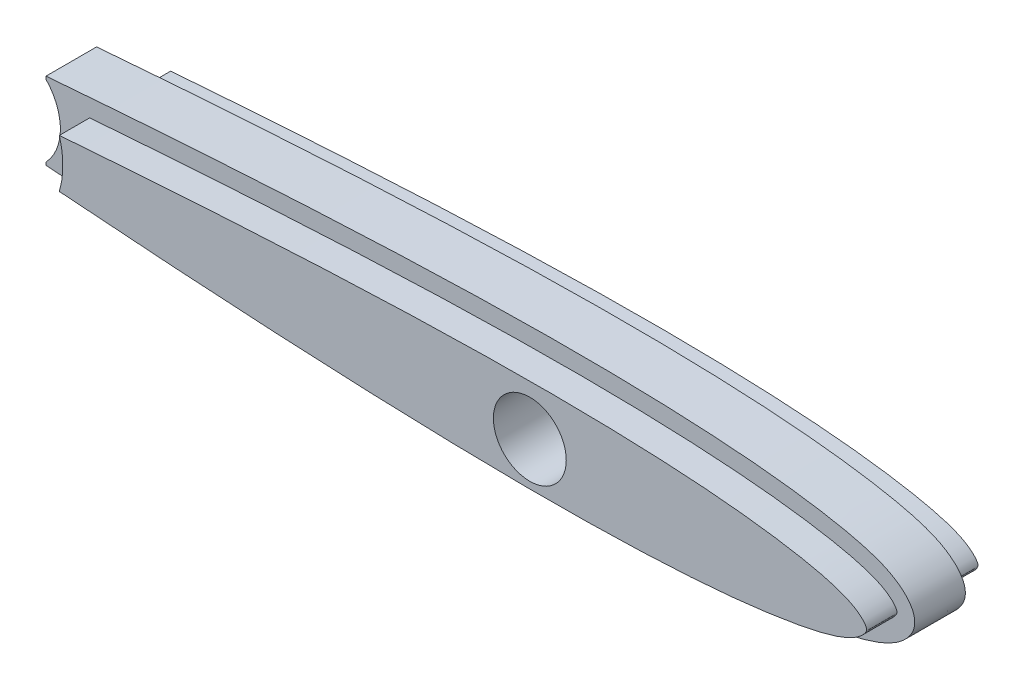
SolidWorks part; units mm, degrees
ref_plane "Front Plane" through (0, 0, 0) normal (0, 0, 1) x (1, 0, 0)
ref_plane "Top Plane" through (0, 0, 0) normal (0, 1, 0) x (1, 0, 0)
ref_plane "Right Plane" through (0, 0, 0) normal (1, 0, 0) x (0, 0, -1)
sketch "Sketch1" plane through (0, 0, 0) normal (0, 0, 1) x (1, 0, 0)
  line L4 (-706.7938, 2.2504) -> (-706.7938, 1.9715)
  line L5 (-706.7938, -5.0985) -> (-706.7938, -5.3802)
  arc A2 (-706.7938, -5.0985) -> (-706.7938, 1.9715) centre (-710.4884, -1.5635) ccw
  spline S2 degree 3 poles (-706.7938, -5.3802) (-704.1764, -5.592) (-696.7883, -6.161) (-687.0049, -6.8148) (-677.4434, -7.3285) (-670.2656, -7.6378) (-663.0802, -7.8569) (-655.8863, -7.9601) (-649.8823, -7.9158) (-645.0737, -7.7768) (-641.4661, -7.6099) (-637.8546, -7.3655) (-634.8408, -7.0787) (-632.4293, -6.7787) (-630.6227, -6.5149) (-628.8123, -6.2021) (-627.3003, -5.8875) (-626.0753, -5.5773) (-625.1447, -5.2998) (-624.2018, -4.9578) (-623.3964, -4.5815) (-622.7483, -4.1895) (-622.2645, -3.8332) (-621.8884, -3.491) (-621.5737, -3.1399) (-621.3353, -2.8044) (-621.1521, -2.4704) (-621.0138, -2.0627) (-620.9486, -1.6664) (-620.9784, -1.2185) (-621.1027, -0.7699) (-621.2898, -0.3987) (-621.521, -0.0562) (-621.8417, 0.3166) (-622.2137, 0.6613) (-622.6971, 1.026) (-623.3445, 1.425) (-624.151, 1.8078) (-625.0951, 2.1542) (-626.0263, 2.4345) (-626.9455, 2.6693) (-628.1602, 2.941) (-629.6699, 3.228) (-631.478, 3.5155) (-633.8879, 3.8423) (-636.9036, 4.1569) (-640.5153, 4.4246) (-644.124, 4.6097) (-647.7316, 4.7298) (-652.5348, 4.8177) (-658.5378, 4.8077) (-665.7281, 4.6591) (-672.9103, 4.4042) (-680.0859, 4.0652) (-689.6443, 3.5193) (-698.5452, 2.9014) (-705.0549, 2.3911) (-706.7938, 2.2504) knots 0.161072 0.161072 0.161072 0.161072 0.19714 0.26286 0.29572 0.32858 0.36144 0.394299 0.427159 0.443589 0.460019 0.476449 0.492879 0.501094 0.509309 0.517524 0.525739 0.529846 0.533954 0.538061 0.542169 0.544222 0.546276 0.54833 0.549357 0.550383 0.55141 0.551924 0.552437 0.552951 0.553464 0.554491 0.555518 0.556545 0.558598 0.560652 0.562706 0.566813 0.570921 0.575028 0.579136 0.583243 0.591458 0.599673 0.607888 0.624318 0.640748 0.657178 0.673608 0.690038 0.722898 0.755757 0.788617 0.821477 0.854337 0.920056 0.944018 0.944018 0.944018 0.944018
extrude "Boss-Extrude1" add sketch "Sketch1" along normal blind 5
sketch "Sketch2" plane through (0, 0, 0) normal (0, 0, -1) x (-1, 0, 0)
  circle A0 centre (655.9929, -1.9195) radius 3.6 construction
  circle A1 centre (655.9929, -1.9195) radius 3.6
extrude "Cut-Extrude1" cut sketch "Sketch2" against normal blind 5
sketch "Sketch3" plane through (0, 0, 5) normal (0, 0, 1) x (1, 0, 0)
  arc A1 (-702.6192, -3.5388) -> (-702.3751, -1.5605) centre (-710.4884, -1.5635) ccw construction
  arc A2 (-702.8119, -4.1898) -> (-702.8111, 1.0606) centre (-710.4884, -1.5635) ccw
  circle A3 centre (-655.9929, -1.9195) radius 3.6 construction
  circle A4 centre (-655.9929, -1.9195) radius 3.6
  spline S0 degree 3 poles (-1458.7742, 1754.4211) (-1395.7984, 224.9146) (-1050.7374, 19.6539) (-690.3603, -5.0851) (-683.4721, -5.506) (-676.464, -5.8734) (-669.4557, -6.1656) (-663.6689, -6.3344) (-659.1295, -6.4119) (-655.8271, -6.4395) (-652.6128, -6.4356) (-649.5004, -6.3942) (-646.5035, -6.3216) (-643.6351, -6.2119) (-640.9073, -6.0692) (-638.3314, -5.89) (-635.9183, -5.6775) (-633.6791, -5.4298) (-631.6233, -5.1516) (-629.7587, -4.8501) (-628.0933, -4.5266) (-626.6323, -4.1822) (-625.3828, -3.8054) (-624.3473, -3.3891) (-623.5355, -2.9298) (-622.9517, -2.4503) (-622.5871, -2.0107) (-622.4112, -1.5647) (-622.5871, -1.1186) (-622.9517, -0.6791) (-623.5355, -0.1995) (-624.3473, 0.2598) (-625.3828, 0.676) (-626.6323, 1.0529) (-628.0933, 1.3972) (-629.7587, 1.7207) (-631.6233, 2.0223) (-633.6791, 2.3005) (-635.9183, 2.5482) (-638.3314, 2.7607) (-640.9073, 2.9399) (-643.6351, 3.0826) (-646.5035, 3.1923) (-649.5004, 3.2649) (-652.6128, 3.3063) (-655.8271, 3.3101) (-659.1295, 3.2826) (-663.6689, 3.2051) (-669.4557, 3.0363) (-676.464, 2.7441) (-683.4721, 2.3767) (-690.3603, 1.9557) (-1049.5872, -22.7043) (-1393.5841, -226.7065) (-1455.9917, -1759.2228) knots -4.752348 -4.752348 -4.752348 -4.752348 0.15349 0.184227 0.21605 0.248408 0.28075 0.312527 0.328033 0.343195 0.357951 0.372242 0.386007 0.399183 0.411723 0.423576 0.434697 0.44504 0.454559 0.463229 0.471015 0.477891 0.483866 0.488952 0.493207 0.496652 0.499261 0.501069 0.502876 0.505486 0.508931 0.513186 0.518272 0.524247 0.531123 0.538909 0.547579 0.557098 0.567441 0.578562 0.590415 0.602955 0.616131 0.629896 0.644187 0.658943 0.674105 0.689611 0.721388 0.75373 0.786088 0.817911 0.848648 5.738628 5.738628 5.738628 5.738628 only from (-702.8119, -4.1898) to (-702.8111, 1.0606) construction
  spline S1 degree 3 poles (-702.8119, -4.1898) (-700.9173, -4.3362) (-696.7938, -4.6434) (-690.3603, -5.0851) (-683.4721, -5.506) (-676.464, -5.8734) (-669.4557, -6.1656) (-663.6689, -6.3344) (-659.1295, -6.4119) (-655.8271, -6.4395) (-652.6128, -6.4356) (-649.5004, -6.3942) (-646.5035, -6.3216) (-643.6351, -6.2119) (-640.9073, -6.0692) (-638.3314, -5.89) (-635.9183, -5.6775) (-633.6791, -5.4298) (-631.6233, -5.1516) (-629.7587, -4.8501) (-628.0933, -4.5266) (-626.6323, -4.1822) (-625.3828, -3.8054) (-624.3473, -3.3891) (-623.5355, -2.9298) (-622.9517, -2.4503) (-622.5871, -2.0107) (-622.4112, -1.5647) (-622.5871, -1.1186) (-622.9517, -0.6791) (-623.5355, -0.1995) (-624.3473, 0.2598) (-625.3828, 0.676) (-626.6323, 1.0529) (-628.0933, 1.3972) (-629.7587, 1.7207) (-631.6233, 2.0223) (-633.6791, 2.3005) (-635.9183, 2.5482) (-638.3314, 2.7607) (-640.9073, 2.9399) (-643.6351, 3.0826) (-646.5035, 3.1923) (-649.5004, 3.2649) (-652.6128, 3.3063) (-655.8271, 3.3101) (-659.1295, 3.2826) (-663.6689, 3.2051) (-669.4557, 3.0363) (-676.464, 2.7441) (-683.4721, 2.3767) (-690.3603, 1.9557) (-696.7935, 1.5141) (-700.9168, 1.207) (-702.8111, 1.0606) knots 0.127353 0.127353 0.127353 0.127353 0.15349 0.184227 0.21605 0.248408 0.28075 0.312527 0.328033 0.343195 0.357951 0.372242 0.386007 0.399183 0.411723 0.423576 0.434697 0.44504 0.454559 0.463229 0.471015 0.477891 0.483866 0.488952 0.493207 0.496652 0.499261 0.501069 0.502876 0.505486 0.508931 0.513186 0.518272 0.524247 0.531123 0.538909 0.547579 0.557098 0.567441 0.578562 0.590415 0.602955 0.616131 0.629896 0.644187 0.658943 0.674105 0.689611 0.721388 0.75373 0.786088 0.817911 0.848648 0.874781 0.874781 0.874781 0.874781
extrude "Boss-Extrude2" add sketch "Sketch3" along normal blind 3
sketch "Sketch4" plane through (0, 0, 0) normal (0, 0, -1) x (-1, 0, 0)
  circle A0 centre (655.9929, -1.9195) radius 3.6 construction
  arc A1 (702.8111, 1.0606) -> (702.8119, -4.1898) centre (710.4884, -1.5635) ccw
  arc A2 (702.8111, 1.0606) -> (702.8119, -4.1898) centre (710.4884, -1.5635) ccw
  circle A3 centre (655.9929, -1.9195) radius 3.6
  spline S1 degree 3 poles (1460.1118, -2759.1755) (1520.2418, -308.2066) (1115.5237, -27.2307) (690.3603, 1.9557) (683.4721, 2.3767) (676.464, 2.7441) (669.4557, 3.0363) (663.6689, 3.2051) (659.1295, 3.2826) (655.8271, 3.3101) (652.6128, 3.3063) (649.5004, 3.2649) (646.5035, 3.1923) (643.6351, 3.0826) (640.9073, 2.9399) (638.3314, 2.7607) (635.9183, 2.5482) (633.6791, 2.3005) (631.6233, 2.0223) (629.7587, 1.7207) (628.0933, 1.3972) (626.6323, 1.0529) (625.3828, 0.676) (624.3473, 0.2598) (623.5355, -0.1995) (622.9517, -0.6791) (622.5871, -1.1186) (622.4112, -1.5647) (622.5871, -2.0107) (622.9517, -2.4503) (623.5355, -2.9298) (624.3473, -3.3891) (625.3828, -3.8054) (626.6323, -4.1822) (628.0933, -4.5266) (629.7587, -4.8501) (631.6233, -5.1516) (633.6791, -5.4298) (635.9183, -5.6775) (638.3314, -5.89) (640.9073, -6.0692) (643.6351, -6.2119) (646.5035, -6.3216) (649.5004, -6.3942) (652.6128, -6.4356) (655.8271, -6.4395) (659.1295, -6.4119) (663.6689, -6.3344) (669.4557, -6.1656) (676.464, -5.8734) (683.4721, -5.506) (690.3603, -5.0851) (1117.011, 24.2034) (1523.0847, 307.0859) (1463.1046, 2754.3608) knots -5.645538 -5.645538 -5.645538 -5.645538 0.153487 0.184223 0.216047 0.248405 0.280746 0.312524 0.328029 0.343192 0.357947 0.372239 0.386003 0.399179 0.41172 0.423573 0.434693 0.445036 0.454556 0.463225 0.471011 0.477887 0.483862 0.488948 0.493204 0.496648 0.499258 0.501066 0.502873 0.505483 0.508927 0.513183 0.518269 0.524244 0.53112 0.538906 0.547575 0.557095 0.567438 0.578558 0.590411 0.602952 0.616128 0.629892 0.644184 0.658939 0.674102 0.689607 0.721385 0.753726 0.786084 0.817908 0.848644 6.668173 6.668173 6.668173 6.668173 only from (702.8111, 1.0606) to (702.8119, -4.1898)
  spline S2 degree 3 poles (702.8111, 1.0606) (700.9168, 1.207) (696.7935, 1.5141) (690.3603, 1.9557) (683.4721, 2.3767) (676.464, 2.7441) (669.4557, 3.0363) (663.6689, 3.2051) (659.1295, 3.2826) (655.8271, 3.3101) (652.6128, 3.3063) (649.5004, 3.2649) (646.5035, 3.1923) (643.6351, 3.0826) (640.9073, 2.9399) (638.3314, 2.7607) (635.9183, 2.5482) (633.6791, 2.3005) (631.6233, 2.0223) (629.7587, 1.7207) (628.0933, 1.3972) (626.6323, 1.0529) (625.3828, 0.676) (624.3473, 0.2598) (623.5355, -0.1995) (622.9517, -0.6791) (622.5871, -1.1186) (622.4112, -1.5647) (622.5871, -2.0107) (622.9517, -2.4503) (623.5355, -2.9298) (624.3473, -3.3891) (625.3828, -3.8054) (626.6323, -4.1822) (628.0933, -4.5266) (629.7587, -4.8501) (631.6233, -5.1516) (633.6791, -5.4298) (635.9183, -5.6775) (638.3314, -5.89) (640.9073, -6.0692) (643.6351, -6.2119) (646.5035, -6.3216) (649.5004, -6.3942) (652.6128, -6.4356) (655.8271, -6.4395) (659.1295, -6.4119) (663.6689, -6.3344) (669.4557, -6.1656) (676.464, -5.8734) (683.4721, -5.506) (690.3603, -5.0851) (696.7938, -4.6434) (700.9173, -4.3362) (702.8119, -4.1898) knots 0.127353 0.127353 0.127353 0.127353 0.153487 0.184223 0.216047 0.248405 0.280746 0.312524 0.328029 0.343192 0.357947 0.372239 0.386003 0.399179 0.41172 0.423573 0.434693 0.445036 0.454556 0.463225 0.471011 0.477887 0.483862 0.488948 0.493204 0.496648 0.499258 0.501066 0.502873 0.505483 0.508927 0.513183 0.518269 0.524244 0.53112 0.538906 0.547575 0.557095 0.567438 0.578558 0.590411 0.602952 0.616128 0.629892 0.644184 0.658939 0.674102 0.689607 0.721385 0.753726 0.786084 0.817908 0.848644 0.874781 0.874781 0.874781 0.874781
  dimension "D1" = 0
extrude "Boss-Extrude3" add sketch "Sketch4" along normal blind 3
sketch "Sketch5" plane through (0, 0, -3) normal (0, 0, -1) x (-1, 0, 0)
  line L2 (706.7938, -5.3802) -> (706.7938, -5.0985)
  line L3 (706.7938, 1.9715) -> (706.7938, 2.2504)
  line L4 (706.7938, -5.3802) -> (706.7938, -5.0985)
  line L5 (706.7938, 1.9715) -> (706.7938, 2.2504)
  arc A2 (702.4766, 0.8356) -> (702.4772, -3.9649) centre (710.4884, -1.5635) ccw
  arc A3 (702.4766, 0.8356) -> (702.4772, -3.9649) centre (710.4884, -1.5635) ccw
  arc A4 (706.7938, 1.9715) -> (706.7938, -5.0985) centre (710.4884, -1.5635) ccw
  arc A5 (706.7938, 1.9715) -> (706.7938, -5.0985) centre (710.4884, -1.5635) ccw
  spline S2 degree 3 poles (1843.7159, 2649.2362) (1372.5351, -266.0132) (1032.1024, -17.1061) (678.7978, 2.3749) (675.4128, 2.5393) (668.6404, 2.8098) (665.2531, 2.917) (658.475, 3.0498) (655.0844, 3.078) (648.2979, 3.0053) (644.9038, 2.9112) (639.8233, 2.621) (638.1312, 2.4986) (634.751, 2.1792) (633.0639, 1.9804) (630.5477, 1.5977) (629.7112, 1.4561) (628.0447, 1.1285) (627.2139, 0.9453) (625.9909, 0.5988) (625.587, 0.4707) (624.7922, 0.1711) (624.3988, -0.0022) (623.8487, -0.3177) (623.6716, -0.4326) (623.3346, -0.6888) (623.1729, -0.8307) (622.9559, -1.0706) (622.8886, -1.1558) (622.804, -1.2931) (622.7781, -1.3403) (622.7348, -1.4396) (622.717, -1.4915) (622.709, -1.5992) (622.7228, -1.6527) (622.7603, -1.7528) (622.7846, -1.8004) (622.8648, -1.9397) (622.9288, -2.0251) (623.1369, -2.2644) (623.2962, -2.4077) (623.6298, -2.6678) (623.8052, -2.7841) (624.3498, -3.1032) (624.7389, -3.2776) (625.5232, -3.5783) (625.9213, -3.7065) (626.7242, -3.9375) (627.1291, -4.0403) (628.3501, -4.3248) (629.1725, -4.485) (630.8241, -4.7726) (631.6512, -4.8988) (634.1352, -5.2407) (635.7949, -5.4173) (639.1193, -5.7021) (640.7838, -5.8118) (645.7827, -6.0697) (649.1232, -6.1521) (655.8065, -6.2041) (659.1455, -6.1704) (665.8205, -6.0299) (669.1563, -5.921) (675.8257, -5.6494) (679.1591, -5.4856) (1033.4659, 14.1921) (1374.5921, 263.2311) (1846.3765, -2650.3425) knots -6.337659 -6.337659 -6.337659 -6.337659 0.125 0.125 0.1875 0.1875 0.25 0.25 0.3125 0.3125 0.375 0.375 0.40625 0.40625 0.4375 0.4375 0.453125 0.453125 0.46875 0.46875 0.476563 0.476563 0.484375 0.484375 0.488281 0.488281 0.492188 0.492188 0.494141 0.494141 0.495117 0.495117 0.496094 0.496094 0.49707 0.49707 0.498047 0.498047 0.5 0.5 0.503906 0.503906 0.507813 0.507813 0.515625 0.515625 0.523438 0.523438 0.53125 0.53125 0.546875 0.546875 0.5625 0.5625 0.59375 0.59375 0.625 0.625 0.6875 0.6875 0.75 0.75 0.8125 0.8125 0.875 0.875 7.457326 7.457326 7.457326 7.457326 only from (702.4766, 0.8356) to (702.4772, -3.9649)
  spline S3 degree 3 poles (702.4766, 0.8356) (695.7145, 1.3561) (688.95, 1.8152) (678.7978, 2.3749) (675.4128, 2.5393) (668.6404, 2.8098) (665.2531, 2.917) (658.475, 3.0498) (655.0844, 3.078) (648.2979, 3.0053) (644.9038, 2.9112) (639.8233, 2.621) (638.1312, 2.4986) (634.751, 2.1792) (633.0639, 1.9804) (630.5477, 1.5977) (629.7112, 1.4561) (628.0447, 1.1285) (627.2139, 0.9453) (625.9909, 0.5988) (625.587, 0.4707) (624.7922, 0.1711) (624.3988, -0.0022) (623.8487, -0.3177) (623.6716, -0.4326) (623.3346, -0.6888) (623.1729, -0.8307) (622.9559, -1.0706) (622.8886, -1.1558) (622.804, -1.2931) (622.7781, -1.3403) (622.7348, -1.4396) (622.717, -1.4915) (622.709, -1.5992) (622.7228, -1.6527) (622.7603, -1.7528) (622.7846, -1.8004) (622.8648, -1.9397) (622.9288, -2.0251) (623.1369, -2.2644) (623.2962, -2.4077) (623.6298, -2.6678) (623.8052, -2.7841) (624.3498, -3.1032) (624.7389, -3.2776) (625.5232, -3.5783) (625.9213, -3.7065) (626.7242, -3.9375) (627.1291, -4.0403) (628.3501, -4.3248) (629.1725, -4.485) (630.8241, -4.7726) (631.6512, -4.8988) (634.1352, -5.2407) (635.7949, -5.4173) (639.1193, -5.7021) (640.7838, -5.8118) (645.7827, -6.0697) (649.1232, -6.1521) (655.8065, -6.2041) (659.1455, -6.1704) (665.8205, -6.0299) (669.1563, -5.921) (675.8257, -5.6494) (679.1591, -5.4856) (689.1568, -4.9304) (695.8183, -4.4774) (702.4772, -3.9649) knots 0 0 0 0 0.125 0.125 0.1875 0.1875 0.25 0.25 0.3125 0.3125 0.375 0.375 0.40625 0.40625 0.4375 0.4375 0.453125 0.453125 0.46875 0.46875 0.476563 0.476563 0.484375 0.484375 0.488281 0.488281 0.492188 0.492188 0.494141 0.494141 0.495117 0.495117 0.496094 0.496094 0.49707 0.49707 0.498047 0.498047 0.5 0.5 0.503906 0.503906 0.507813 0.507813 0.515625 0.515625 0.523438 0.523438 0.53125 0.53125 0.546875 0.546875 0.5625 0.5625 0.59375 0.59375 0.625 0.625 0.6875 0.6875 0.75 0.75 0.8125 0.8125 0.875 0.875 1 1 1 1
  spline S4 degree 3 poles (1427.9881, -2784.3302) (1470.56, -267.9599) (1089.4618, -24.2364) (689.6443, 3.5193) (680.0859, 4.0652) (672.9103, 4.4042) (665.7281, 4.6591) (658.5378, 4.8077) (652.5348, 4.8177) (647.7316, 4.7298) (644.124, 4.6097) (640.5153, 4.4246) (636.9036, 4.1569) (633.8879, 3.8423) (631.478, 3.5155) (629.6699, 3.228) (628.1602, 2.941) (626.9455, 2.6693) (626.0263, 2.4345) (625.0951, 2.1542) (624.151, 1.8078) (623.3445, 1.425) (622.6971, 1.026) (622.2137, 0.6613) (621.8417, 0.3166) (621.521, -0.0562) (621.2898, -0.3987) (621.1027, -0.7699) (620.9784, -1.2185) (620.9486, -1.6664) (621.0138, -2.0627) (621.1521, -2.4704) (621.3353, -2.8044) (621.5737, -3.1399) (621.8884, -3.491) (622.2645, -3.8332) (622.7483, -4.1895) (623.3964, -4.5815) (624.2018, -4.9578) (625.1447, -5.2998) (626.0753, -5.5773) (627.3003, -5.8875) (628.8123, -6.2021) (630.6227, -6.5149) (632.4293, -6.7787) (634.8408, -7.0787) (637.8546, -7.3655) (641.4661, -7.6099) (645.0737, -7.7768) (649.8823, -7.9158) (655.8863, -7.9601) (663.0802, -7.8569) (670.2656, -7.6378) (677.4434, -7.3285) (687.0049, -6.8148) (1039.6939, 16.7536) (1372.7561, 207.9404) (2635.5245, 2240.3202) knots -5.220774 -5.220774 -5.220774 -5.220774 0.185033 0.250752 0.283612 0.316472 0.349332 0.382192 0.415052 0.431481 0.447911 0.464341 0.480771 0.497201 0.505416 0.513631 0.521846 0.525953 0.530061 0.534168 0.538276 0.542383 0.544437 0.546491 0.548545 0.549571 0.550598 0.551625 0.552139 0.552652 0.553165 0.553679 0.554706 0.555733 0.55676 0.558813 0.560867 0.562921 0.567028 0.571136 0.575243 0.579351 0.587566 0.595781 0.603995 0.61221 0.62864 0.64507 0.6615 0.67793 0.71079 0.74365 0.77651 0.809369 0.842229 0.907949 5.663443 5.663443 5.663443 5.663443 only from (706.7938, 2.2504) to (706.7938, -5.3802)
  spline S5 degree 3 poles (706.7938, 2.2504) (705.0549, 2.3911) (698.5452, 2.9014) (689.6443, 3.5193) (680.0859, 4.0652) (672.9103, 4.4042) (665.7281, 4.6591) (658.5378, 4.8077) (652.5348, 4.8177) (647.7316, 4.7298) (644.124, 4.6097) (640.5153, 4.4246) (636.9036, 4.1569) (633.8879, 3.8423) (631.478, 3.5155) (629.6699, 3.228) (628.1602, 2.941) (626.9455, 2.6693) (626.0263, 2.4345) (625.0951, 2.1542) (624.151, 1.8078) (623.3445, 1.425) (622.6971, 1.026) (622.2137, 0.6613) (621.8417, 0.3166) (621.521, -0.0562) (621.2898, -0.3987) (621.1027, -0.7699) (620.9784, -1.2185) (620.9486, -1.6664) (621.0138, -2.0627) (621.1521, -2.4704) (621.3353, -2.8044) (621.5737, -3.1399) (621.8884, -3.491) (622.2645, -3.8332) (622.7483, -4.1895) (623.3964, -4.5815) (624.2018, -4.9578) (625.1447, -5.2998) (626.0753, -5.5773) (627.3003, -5.8875) (628.8123, -6.2021) (630.6227, -6.5149) (632.4293, -6.7787) (634.8408, -7.0787) (637.8546, -7.3655) (641.4661, -7.6099) (645.0737, -7.7768) (649.8823, -7.9158) (655.8863, -7.9601) (663.0802, -7.8569) (670.2656, -7.6378) (677.4434, -7.3285) (687.0049, -6.8148) (696.7883, -6.161) (704.1764, -5.592) (706.7938, -5.3802) knots 0.161072 0.161072 0.161072 0.161072 0.185033 0.250752 0.283612 0.316472 0.349332 0.382192 0.415052 0.431481 0.447911 0.464341 0.480771 0.497201 0.505416 0.513631 0.521846 0.525953 0.530061 0.534168 0.538276 0.542383 0.544437 0.546491 0.548545 0.549571 0.550598 0.551625 0.552139 0.552652 0.553165 0.553679 0.554706 0.555733 0.55676 0.558813 0.560867 0.562921 0.567028 0.571136 0.575243 0.579351 0.587566 0.595781 0.603995 0.61221 0.62864 0.64507 0.6615 0.67793 0.71079 0.74365 0.77651 0.809369 0.842229 0.907949 0.944018 0.944018 0.944018 0.944018
  dimension "D1" = 0.25
  dimension "D2" = 0
extrude "Cut-Extrude2" cut sketch "Sketch5" against normal up to surface (3 mm away) up to face at (-706.4391, -2.518, 0)
sketch "Sketch6" plane through (0, 0, 8) normal (0, 0, 1) x (1, 0, 0)
  line L2 (-706.7938, -5.0985) -> (-706.7938, -5.3802)
  line L3 (-706.7938, 2.2504) -> (-706.7938, 1.9715)
  line L4 (-706.7938, -5.0985) -> (-706.7938, -5.3802)
  line L5 (-706.7938, 2.2504) -> (-706.7938, 1.9715)
  arc A1 (-702.4772, -3.9649) -> (-702.4766, 0.8356) centre (-710.4884, -1.5635) ccw
  arc A2 (-702.4772, -3.9649) -> (-702.4766, 0.8356) centre (-710.4884, -1.5635) ccw
  arc A3 (-706.7938, -5.0985) -> (-706.7938, 1.9715) centre (-710.4884, -1.5635) ccw
  arc A4 (-706.7938, -5.0985) -> (-706.7938, 1.9715) centre (-710.4884, -1.5635) ccw
  spline S1 degree 3 poles (-1846.3779, -2650.3512) (-1374.5928, 263.2316) (-1033.4663, 14.1921) (-679.1591, -5.4856) (-675.8257, -5.6494) (-669.1563, -5.921) (-665.8205, -6.0299) (-659.1455, -6.1704) (-655.8065, -6.2041) (-649.1232, -6.1521) (-645.7827, -6.0697) (-640.7838, -5.8118) (-639.1193, -5.7021) (-635.7949, -5.4173) (-634.1352, -5.2407) (-631.6512, -4.8988) (-630.8241, -4.7726) (-629.1725, -4.485) (-628.3501, -4.3248) (-627.1291, -4.0403) (-626.7242, -3.9375) (-625.9213, -3.7065) (-625.5232, -3.5783) (-624.7389, -3.2776) (-624.3498, -3.1032) (-623.8052, -2.7841) (-623.6298, -2.6678) (-623.2962, -2.4077) (-623.1369, -2.2644) (-622.9288, -2.0251) (-622.8648, -1.9397) (-622.7846, -1.8004) (-622.7603, -1.7528) (-622.7228, -1.6527) (-622.709, -1.5992) (-622.717, -1.4915) (-622.7348, -1.4396) (-622.7781, -1.3403) (-622.804, -1.2931) (-622.8886, -1.1558) (-622.9559, -1.0706) (-623.1729, -0.8307) (-623.3346, -0.6888) (-623.6716, -0.4326) (-623.8487, -0.3177) (-624.3988, -0.0022) (-624.7922, 0.1711) (-625.587, 0.4707) (-625.9909, 0.5988) (-627.2139, 0.9453) (-628.0447, 1.1285) (-629.7112, 1.4561) (-630.5477, 1.5977) (-633.0639, 1.9804) (-634.751, 2.1792) (-638.1312, 2.4986) (-639.8233, 2.621) (-644.9038, 2.9112) (-648.2979, 3.0053) (-655.0844, 3.078) (-658.475, 3.0498) (-665.2531, 2.917) (-668.6404, 2.8098) (-675.4128, 2.5393) (-678.7978, 2.3749) (-1032.1042, -17.1062) (-1372.5384, -266.0156) (-1843.7229, 2649.2791) knots -6.457333 -6.457333 -6.457333 -6.457333 0.125 0.125 0.1875 0.1875 0.25 0.25 0.3125 0.3125 0.375 0.375 0.40625 0.40625 0.4375 0.4375 0.453125 0.453125 0.46875 0.46875 0.476562 0.476562 0.484375 0.484375 0.492187 0.492187 0.496094 0.496094 0.5 0.5 0.501953 0.501953 0.50293 0.50293 0.503906 0.503906 0.504883 0.504883 0.505859 0.505859 0.507812 0.507812 0.511719 0.511719 0.515625 0.515625 0.523437 0.523437 0.53125 0.53125 0.546875 0.546875 0.5625 0.5625 0.59375 0.59375 0.625 0.625 0.6875 0.6875 0.75 0.75 0.8125 0.8125 0.875 0.875 7.337691 7.337691 7.337691 7.337691 only from (-702.4772, -3.9649) to (-702.4766, 0.8356)
  spline S2 degree 3 poles (-702.4772, -3.9649) (-695.8183, -4.4774) (-689.1568, -4.9304) (-679.1591, -5.4856) (-675.8257, -5.6494) (-669.1563, -5.921) (-665.8205, -6.0299) (-659.1455, -6.1704) (-655.8065, -6.2041) (-649.1232, -6.1521) (-645.7827, -6.0697) (-640.7838, -5.8118) (-639.1193, -5.7021) (-635.7949, -5.4173) (-634.1352, -5.2407) (-631.6512, -4.8988) (-630.8241, -4.7726) (-629.1725, -4.485) (-628.3501, -4.3248) (-627.1291, -4.0403) (-626.7242, -3.9375) (-625.9213, -3.7065) (-625.5232, -3.5783) (-624.7389, -3.2776) (-624.3498, -3.1032) (-623.8052, -2.7841) (-623.6298, -2.6678) (-623.2962, -2.4077) (-623.1369, -2.2644) (-622.9288, -2.0251) (-622.8648, -1.9397) (-622.7846, -1.8004) (-622.7603, -1.7528) (-622.7228, -1.6527) (-622.709, -1.5992) (-622.717, -1.4915) (-622.7348, -1.4396) (-622.7781, -1.3403) (-622.804, -1.2931) (-622.8886, -1.1558) (-622.9559, -1.0706) (-623.1729, -0.8307) (-623.3346, -0.6888) (-623.6716, -0.4326) (-623.8487, -0.3177) (-624.3988, -0.0022) (-624.7922, 0.1711) (-625.587, 0.4707) (-625.9909, 0.5988) (-627.2139, 0.9453) (-628.0447, 1.1285) (-629.7112, 1.4561) (-630.5477, 1.5977) (-633.0639, 1.9804) (-634.751, 2.1792) (-638.1312, 2.4986) (-639.8233, 2.621) (-644.9038, 2.9112) (-648.2979, 3.0053) (-655.0844, 3.078) (-658.475, 3.0498) (-665.2531, 2.917) (-668.6404, 2.8098) (-675.4128, 2.5393) (-678.7978, 2.3749) (-688.95, 1.8152) (-695.7145, 1.3561) (-702.4766, 0.8356) knots 0 0 0 0 0.125 0.125 0.1875 0.1875 0.25 0.25 0.3125 0.3125 0.375 0.375 0.40625 0.40625 0.4375 0.4375 0.453125 0.453125 0.46875 0.46875 0.476562 0.476562 0.484375 0.484375 0.492187 0.492187 0.496094 0.496094 0.5 0.5 0.501953 0.501953 0.50293 0.50293 0.503906 0.503906 0.504883 0.504883 0.505859 0.505859 0.507812 0.507812 0.511719 0.511719 0.515625 0.515625 0.523437 0.523437 0.53125 0.53125 0.546875 0.546875 0.5625 0.5625 0.59375 0.59375 0.625 0.625 0.6875 0.6875 0.75 0.75 0.8125 0.8125 0.875 0.875 1 1 1 1
  spline S3 degree 3 poles (-2635.5211, 2240.3148) (-1372.7556, 207.9401) (-1039.6936, 16.7536) (-687.0049, -6.8148) (-677.4434, -7.3285) (-670.2656, -7.6378) (-663.0802, -7.8569) (-655.8863, -7.9601) (-649.8823, -7.9158) (-645.0737, -7.7768) (-641.4661, -7.6099) (-637.8546, -7.3655) (-634.8408, -7.0787) (-632.4293, -6.7787) (-630.6227, -6.5149) (-628.8123, -6.2021) (-627.3003, -5.8875) (-626.0753, -5.5773) (-625.1447, -5.2998) (-624.2018, -4.9578) (-623.3964, -4.5815) (-622.7483, -4.1895) (-622.2645, -3.8332) (-621.8884, -3.491) (-621.5737, -3.1399) (-621.3353, -2.8044) (-621.1521, -2.4704) (-621.0138, -2.0627) (-620.9486, -1.6664) (-620.9784, -1.2185) (-621.1027, -0.7699) (-621.2898, -0.3987) (-621.521, -0.0562) (-621.8417, 0.3166) (-622.2137, 0.6613) (-622.6971, 1.026) (-623.3445, 1.425) (-624.151, 1.8078) (-625.0951, 2.1542) (-626.0263, 2.4345) (-626.9455, 2.6693) (-628.1602, 2.941) (-629.6699, 3.228) (-631.478, 3.5155) (-633.8879, 3.8423) (-636.9036, 4.1569) (-640.5153, 4.4246) (-644.124, 4.6097) (-647.7316, 4.7298) (-652.5348, 4.8177) (-658.5378, 4.8077) (-665.7281, 4.6591) (-672.9103, 4.4042) (-680.0859, 4.0652) (-689.6443, 3.5193) (-1089.4628, -24.2365) (-1470.5619, -267.9611) (-1427.9877, -2784.3493) knots -4.558349 -4.558349 -4.558349 -4.558349 0.19714 0.26286 0.29572 0.32858 0.36144 0.394299 0.427159 0.443589 0.460019 0.476449 0.492879 0.501094 0.509309 0.517524 0.525739 0.529846 0.533954 0.538061 0.542169 0.544222 0.546276 0.54833 0.549357 0.550383 0.55141 0.551924 0.552437 0.552951 0.553464 0.554491 0.555518 0.556545 0.558598 0.560652 0.562706 0.566813 0.570921 0.575028 0.579136 0.583243 0.591458 0.599673 0.607888 0.624318 0.640748 0.657178 0.673608 0.690038 0.722898 0.755757 0.788617 0.821477 0.854337 0.920056 6.325877 6.325877 6.325877 6.325877 only from (-706.7938, -5.3802) to (-706.7938, 2.2504)
  spline S4 degree 3 poles (-706.7938, -5.3802) (-704.1764, -5.592) (-696.7883, -6.161) (-687.0049, -6.8148) (-677.4434, -7.3285) (-670.2656, -7.6378) (-663.0802, -7.8569) (-655.8863, -7.9601) (-649.8823, -7.9158) (-645.0737, -7.7768) (-641.4661, -7.6099) (-637.8546, -7.3655) (-634.8408, -7.0787) (-632.4293, -6.7787) (-630.6227, -6.5149) (-628.8123, -6.2021) (-627.3003, -5.8875) (-626.0753, -5.5773) (-625.1447, -5.2998) (-624.2018, -4.9578) (-623.3964, -4.5815) (-622.7483, -4.1895) (-622.2645, -3.8332) (-621.8884, -3.491) (-621.5737, -3.1399) (-621.3353, -2.8044) (-621.1521, -2.4704) (-621.0138, -2.0627) (-620.9486, -1.6664) (-620.9784, -1.2185) (-621.1027, -0.7699) (-621.2898, -0.3987) (-621.521, -0.0562) (-621.8417, 0.3166) (-622.2137, 0.6613) (-622.6971, 1.026) (-623.3445, 1.425) (-624.151, 1.8078) (-625.0951, 2.1542) (-626.0263, 2.4345) (-626.9455, 2.6693) (-628.1602, 2.941) (-629.6699, 3.228) (-631.478, 3.5155) (-633.8879, 3.8423) (-636.9036, 4.1569) (-640.5153, 4.4246) (-644.124, 4.6097) (-647.7316, 4.7298) (-652.5348, 4.8177) (-658.5378, 4.8077) (-665.7281, 4.6591) (-672.9103, 4.4042) (-680.0859, 4.0652) (-689.6443, 3.5193) (-698.5452, 2.9014) (-705.0549, 2.3911) (-706.7938, 2.2504) knots 0.161072 0.161072 0.161072 0.161072 0.19714 0.26286 0.29572 0.32858 0.36144 0.394299 0.427159 0.443589 0.460019 0.476449 0.492879 0.501094 0.509309 0.517524 0.525739 0.529846 0.533954 0.538061 0.542169 0.544222 0.546276 0.54833 0.549357 0.550383 0.55141 0.551924 0.552437 0.552951 0.553464 0.554491 0.555518 0.556545 0.558598 0.560652 0.562706 0.566813 0.570921 0.575028 0.579136 0.583243 0.591458 0.599673 0.607888 0.624318 0.640748 0.657178 0.673608 0.690038 0.722898 0.755757 0.788617 0.821477 0.854337 0.920056 0.944018 0.944018 0.944018 0.944018
  dimension "D1" = 0
  dimension "D2" = 0
extrude "Cut-Extrude3" cut sketch "Sketch6" against normal up to surface (3 mm away) up to face at (-706.4391, -2.518, 5)
